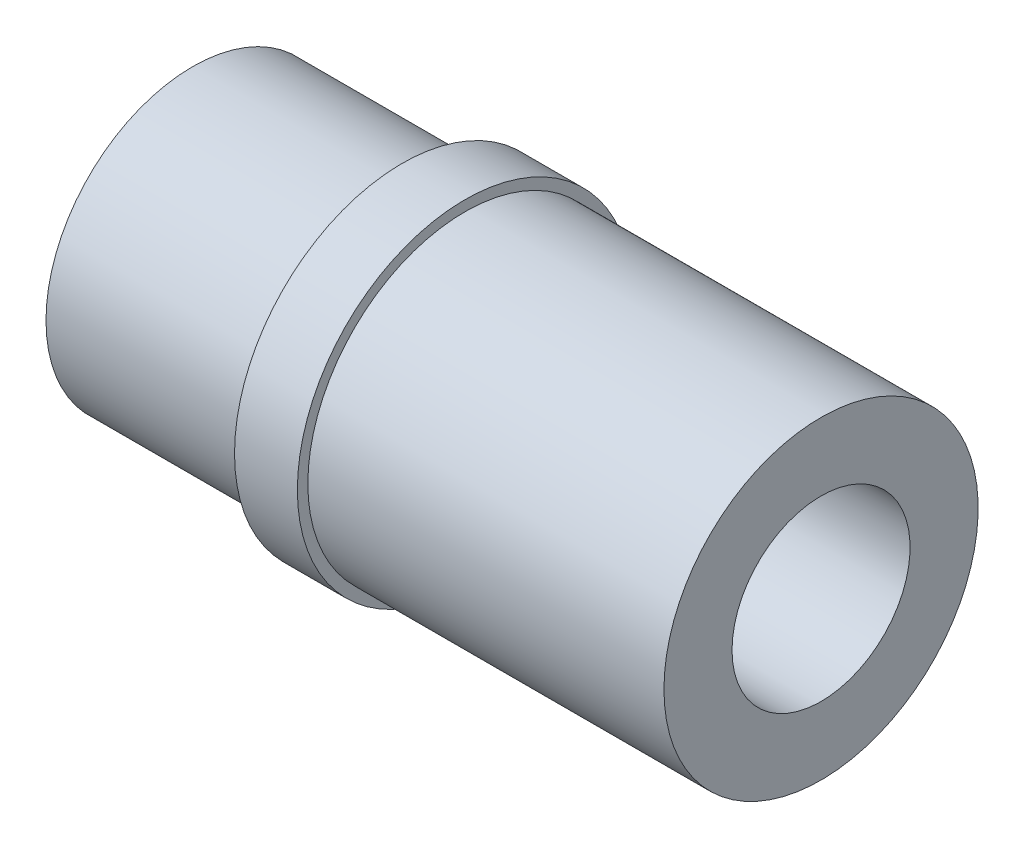
SolidWorks part; units mm, degrees
material "Plain Carbon Steel"
ref_plane "Front Plane" through (0, 0, 0) normal (0, 0, 1) x (1, 0, 0)
ref_plane "Top Plane" through (0, 0, 0) normal (0, 1, 0) x (1, 0, 0)
ref_plane "Right Plane" through (0, 0, 0) normal (1, 0, 0) x (0, 0, -1)
sketch "Sketch1" plane through (0, 0, 0) normal (0, 0, 1) x (1, 0, 0)
  line L0 (0, 0) -> (0, 5.5) construction
  line L1 (0, 5.5) -> (0, 7)
  line L2 (0, 7) -> (10, 7)
  line L3 (10, 7) -> (10, 8)
  line L4 (10, 8) -> (13, 8)
  line L5 (13, 8) -> (13, 7.5)
  line L6 (13, 7.5) -> (30, 7.5)
  line L7 (30, 7.5) -> (30, 4.25)
  line L8 (30, 4.25) -> (8.883, 4.25)
  line L9 (0, 5.5) -> (8.883, 4.25)
  line L10 (0, 0) -> (30, 0) construction
  point P4 (0, 0)
  point P13 (25.4154, 3.6974)
  point P14 (12.0256, 4.25)
  dimension "D1" = 14
  dimension "D2" = 15
  dimension "D3" = 16
  dimension "D4" = 17
  dimension "D5" = 8.5
  dimension "D6" = 8.01
  dimension "D7" = 11
  dimension "D8" = 10
  dimension "D9" = 30
revolve "Revolve1" add sketch "Sketch1" angle 360 about L10
